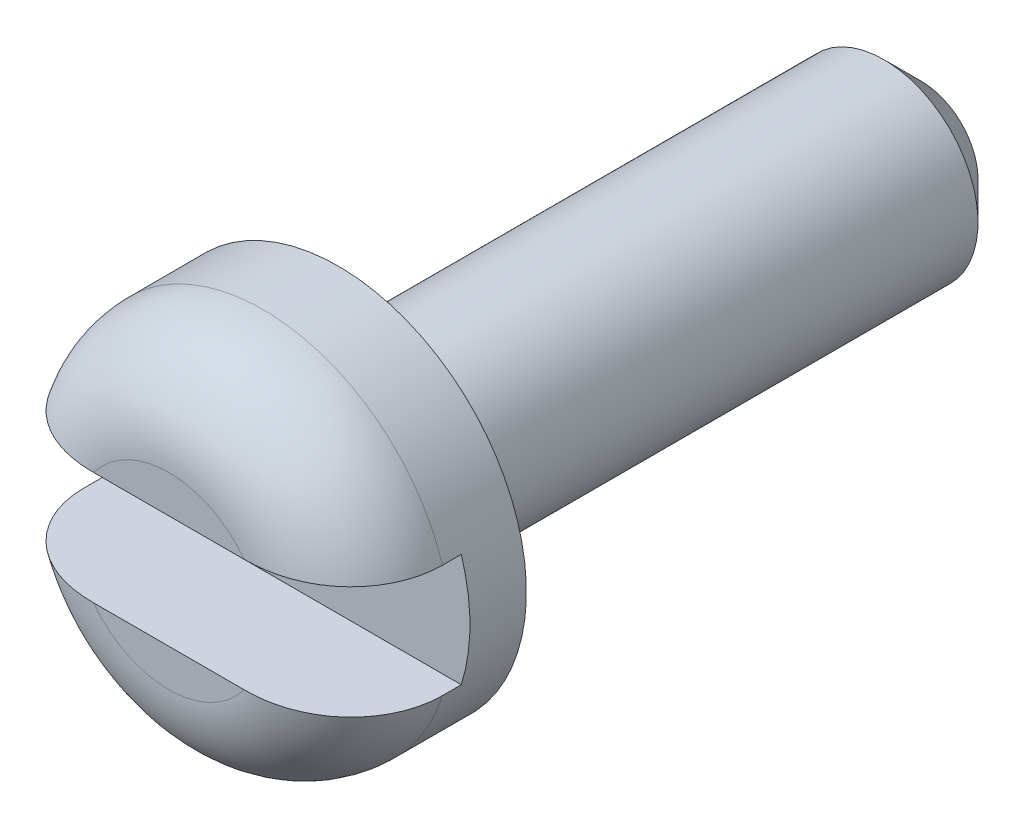
SolidWorks part; units mm, degrees
material "Простая углеродистая сталь"
ref_plane "Спереди" through (0, 0, 0) normal (0, 0, 1) x (1, 0, 0)
ref_plane "Сверху" through (0, 0, 0) normal (0, 1, 0) x (1, 0, 0)
ref_plane "Справа" through (0, 0, 0) normal (1, 0, 0) x (0, 0, -1)
sketch "Эскиз1" plane through (0, 0, 0) normal (0, 1, 0) x (1, 0, 0)
  line L0 (0, 0) -> (-2, 0)
  line L1 (-2, 0) -> (-2, 1.8)
  line L2 (-2, 1.8) -> (-1, 1.8)
  line L3 (-1, 1.8) -> (-1, 8)
  line L4 (-1, 8) -> (0, 8)
  line L5 (0, 8) -> (0, 0)
  dimension "D1" = 2
  dimension "D2" = 1.8
  dimension "D3" = 8
  dimension "D4" = 1
revolve "Повернуть1" add sketch "Эскиз1" angle 360 about L5
sketch "Эскиз2" plane through (0, 0, 0) normal (1, 0, 0) x (0, 0, -1)
  line L0 (0, 0) -> (22.6818, 0) construction
  line L1 (0, -0.6) -> (0, 0.6)
  line L2 (0, 0.6) -> (1.2, 0.6)
  line L3 (0, -0.6) -> (1.2, -0.6)
  line L4 (1.2, 0.6) -> (1.2, -0.6)
  point P7 (0, 0)
  point P10 (1.2, 0)
  dimension "D1" = 1.2
  dimension "D2" = 1.2
extrude "Вырез-Вытянуть1" cut sketch "Эскиз2" against normal through all both and the other way through all
chamfer "Фаска1" distance 0.4 angle 45 1 edges at (-1, 0, -8)
fillet "Скругление1" radius 1 2 edges at (0, -2, 0) (0, 2, 0)
fillet "Скругление2" radius 0.4 1 edges at (-1, 0, -1.8)
